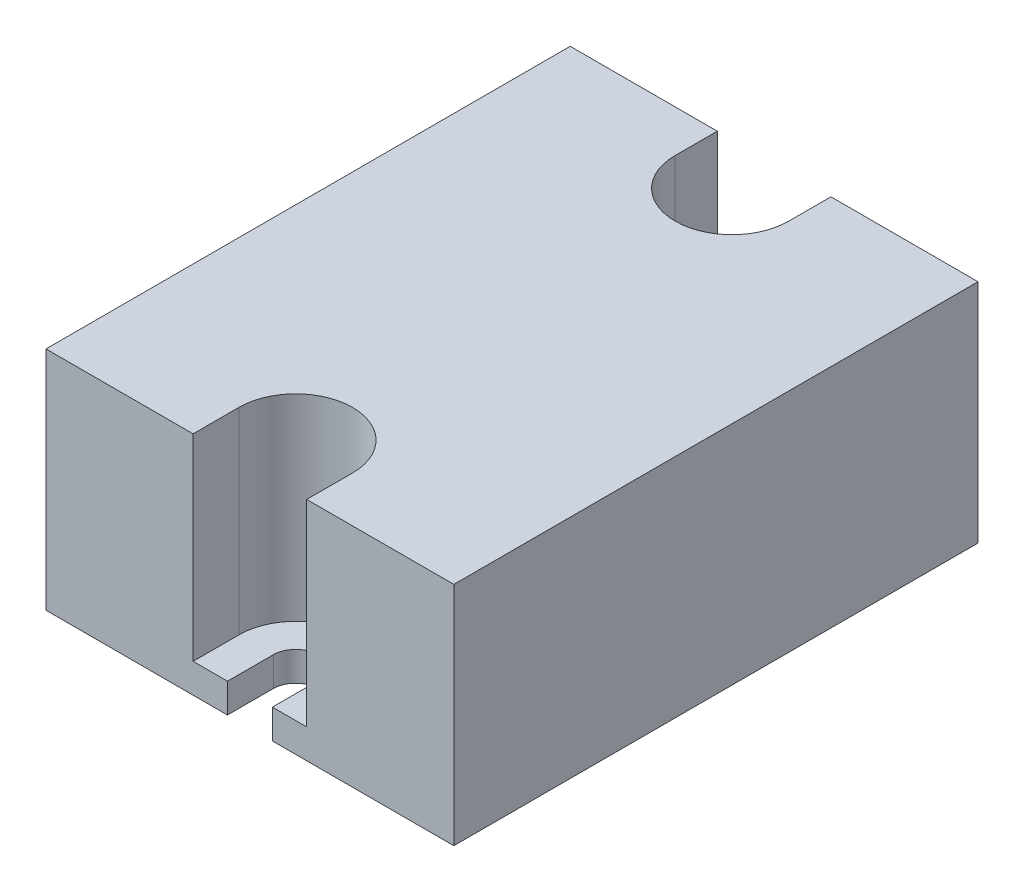
SolidWorks part; units mm, degrees
ref_plane "Front" through (0, 0, 0) normal (0, 0, 1) x (1, 0, 0)
ref_plane "Top" through (0, 0, 0) normal (0, 1, 0) x (1, 0, 0)
ref_plane "Right" through (0, 0, 0) normal (1, 0, 0) x (0, 0, -1)
sketch "Sketch1" plane through (0, 0, 0) normal (0, 1, 0) x (1, 0, 0)
  line L0 (0.0023, 57.1884) -> (44.5023, 57.1884) construction
  line L1 (0, 0) -> (19.8, 0)
  line L2 (19.8, 0) -> (19.8, 5)
  line L3 (0, 0) -> (0, 57.2)
  line L4 (0, 57.2) -> (16.05, 57.2)
  line L5 (16.05, 57.2) -> (28.45, 57.2)
  line L6 (22.25, 62.2047) -> (22.25, 0) construction
  line L7 (25.4952, 7.45) -> (19.0048, 7.45) construction
  line L8 (44.5, 57.2) -> (28.45, 57.2)
  line L9 (44.5, 0) -> (44.5, 57.2)
  line L10 (24.7, 0) -> (24.7, 5)
  line L11 (44.5, 0) -> (24.7, 0)
  arc A0 (24.7, 5) -> (19.8, 5) centre (22.25, 5) ccw
  circle A1 centre (22.25, 52.6) radius 2.45
  point P18 (22.25, 57.2)
  dimension "D5" = 47.6
  dimension "D7" = 4.9
  dimension "D1" = 44.5
  dimension "D2" = 57.2
  dimension "D3" = 6.2
  dimension "D4" = 22.25
  dimension "D6" = 2.45
  dimension "D8" = 5
extrude "Boss-Extrude1" add sketch "Sketch1" along normal blind 3.2
sketch "Sketch2" plane through (0, 3.2, 0) normal (0, 1, 0) x (1, 0, 0)
  line L0 (0, 0) -> (0, 57.2) construction
  line L1 (0, 0) -> (0, 57.2)
  line L2 (0, 57.2) -> (16.05, 57.2)
  line L3 (16.05, 57.2) -> (16.05, 52.6)
  line L4 (0, 0) -> (16.05, 0)
  line L5 (29.6682, 11.2) -> (14.8318, 11.2) construction
  line L6 (0, 0) -> (19.8, 0) construction
  line L7 (16.05, 0) -> (16.05, 5)
  line L8 (16.05, 5) -> (19.8, 5) construction
  line L9 (22.25, 62.2047) -> (22.25, 0) construction
  line L10 (16.05, 52.6) -> (22.25, 52.6) construction
  line L11 (29.378, 46.4) -> (15.122, 46.4) construction
  line L12 (22.25, 62.2047) -> (22.25, 0) construction
  line L13 (28.45, 52.6) -> (22.25, 52.6) construction
  line L14 (28.45, 5) -> (24.7, 5) construction
  line L15 (28.45, 0) -> (28.45, 5)
  line L16 (44.5, 0) -> (28.45, 0)
  line L17 (28.45, 57.2) -> (28.45, 52.6)
  line L18 (44.5, 57.2) -> (28.45, 57.2)
  line L19 (44.5, 0) -> (44.5, 57.2)
  arc A0 (16.05, 5) -> (28.45, 5) centre (22.25, 5) cw
  arc A1 (16.05, 52.6) -> (28.45, 52.6) centre (22.25, 52.6) ccw
extrude "Boss-Extrude2" add sketch "Sketch2" along normal blind 21.5
